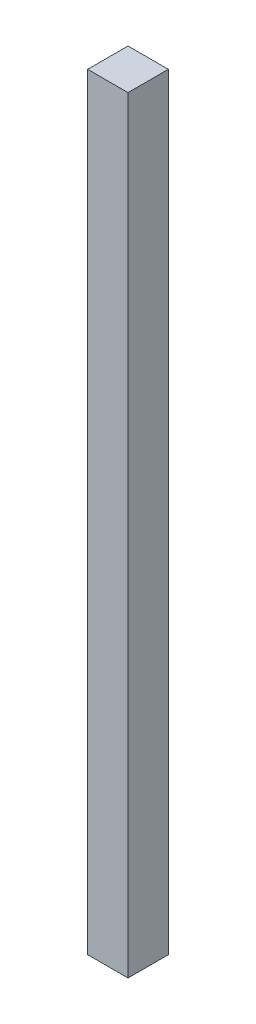
SolidWorks part; units mm, degrees
ref_plane "Front Plane" through (0, 0, 0) normal (0, 0, 1) x (1, 0, 0)
ref_plane "Top Plane" through (0, 0, 0) normal (0, 1, 0) x (1, 0, 0)
ref_plane "Right Plane" through (0, 0, 0) normal (1, 0, 0) x (0, 0, -1)
sketch "Sketch1" plane through (0, 0, 0) normal (0, 1, 0) x (1, 0, 0)
  line L1 (0, 0) -> (10, 0)
  line L2 (0, 0) -> (0, 10)
  line L3 (0, 10) -> (10, 10)
  line L4 (10, 0) -> (10, 10)
  dimension "D1" = 10
  dimension "w" = 10
extrude "Boss-Extrude1" add sketch "Sketch1" along normal blind 190
